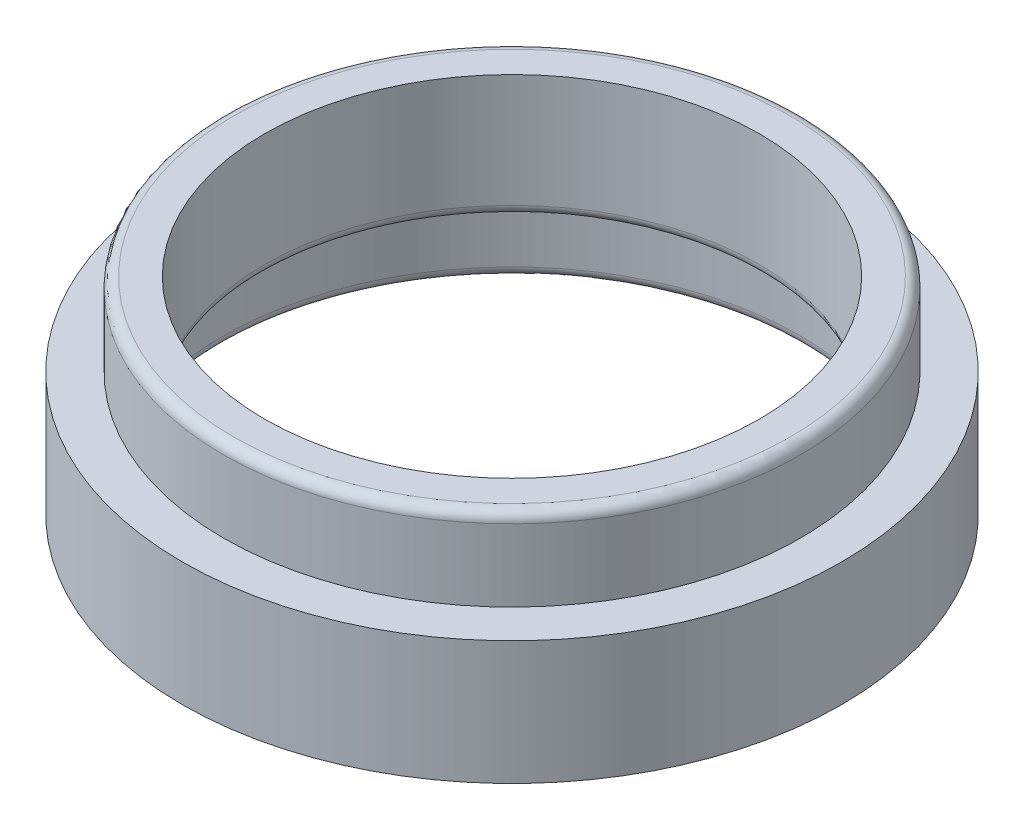
SolidWorks part; units mm, degrees
material "PLA Black"
ref_plane "Front Plane" through (0, 0, 0) normal (0, 0, 1) x (1, 0, 0)
ref_plane "Top Plane" through (0, 0, 0) normal (0, 1, 0) x (1, 0, 0)
ref_plane "Right Plane" through (0, 0, 0) normal (1, 0, 0) x (0, 0, -1)
sketch "Sketch1" plane through (0, 0, 0) normal (1, 0, 0) x (0, 0, -1)
  line L0 (0, -32.3252) -> (0, 32.3252) construction
  line L1 (22.225, 11.1125) -> (22.225, 4.7625)
  line L2 (22.225, 4.7625) -> (25.4, 4.7625)
  line L3 (25.4, 4.7625) -> (25.4, -4.7625)
  line L4 (25.4, -4.7625) -> (22.225, -4.7625)
  line L5 (22.225, -4.7625) -> (22.225, 1.5875)
  line L6 (22.225, 1.5875) -> (19.05, 1.5875)
  line L8 (19.05, 11.1125) -> (22.225, 11.1125)
  line L13 (19.05, 1.5875) -> (19.05, 11.1125)
  point P4 (0, 0)
  point P12 (25.4, 0)
  dimension "D1" = 3.175
  dimension "D2" = 3.175
  dimension "D3" = 6.35
  dimension "D4" = 50.8
revolve "Revolve1" add sketch "Sketch1" angle 360 about L0
fillet "Fillet1" radius 0.7937 4 edges at (0, 1.5875, -22.225) (0, -4.7625, -22.225) (0, 11.1125, -22.225) (0, 1.5875, -19.05)
